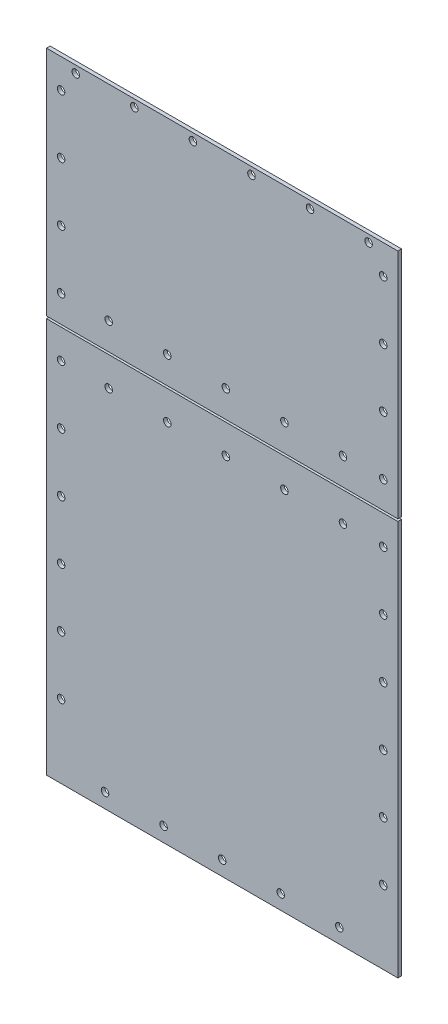
SolidWorks part; units mm, degrees
material "Copper"
ref_plane "Front Plane" through (0, 0, 0) normal (0, 0, 1) x (1, 0, 0)
ref_plane "Top Plane" through (0, 0, 0) normal (0, 1, 0) x (1, 0, 0)
ref_plane "Right Plane" through (0, 0, 0) normal (1, 0, 0) x (0, 0, -1)
sketch "Sketch1" plane through (0, 0, 0) normal (0, 0, 1) x (1, 0, 0)
  line L0 (0, -100.6) -> (152.4, -100.6)
  line L1 (0, 0) -> (152.4, 0)
  line L2 (0, 0) -> (0, -273.05)
  line L3 (0, -273.05) -> (152.4, -273.05)
  line L4 (152.4, 0) -> (152.4, -273.05)
  line L5 (0, -101.6) -> (152.4, -101.6)
  circle A0 centre (6.35, -12.7) radius 1.632
  circle A1 centre (146.05, -12.7) radius 1.632
  circle A2 centre (146.05, -38.1) radius 1.632
  circle A3 centre (146.05, -63.5) radius 1.632
  circle A4 centre (146.05, -88.9) radius 1.632
  circle A5 centre (146.05, -114.3) radius 1.632
  circle A6 centre (146.05, -139.7) radius 1.632
  circle A7 centre (146.05, -165.1) radius 1.632
  circle A8 centre (146.05, -190.5) radius 1.632
  circle A9 centre (146.05, -215.9) radius 1.632
  circle A10 centre (146.05, -241.3) radius 1.632
  circle A11 centre (6.35, -38.1) radius 1.6319
  circle A12 centre (6.35, -63.5) radius 1.6319
  circle A13 centre (6.35, -88.9) radius 1.6319
  circle A14 centre (6.35, -114.3) radius 1.6319
  circle A15 centre (6.35, -139.7) radius 1.6319
  circle A16 centre (6.35, -165.1) radius 1.632
  circle A17 centre (6.35, -190.5) radius 1.632
  circle A18 centre (6.35, -215.9) radius 1.632
  circle A19 centre (6.35, -241.3) radius 1.632
  circle A20 centre (12.7, -3.175) radius 1.632
  circle A21 centre (38.1, -3.175) radius 1.632
  circle A22 centre (63.5, -3.175) radius 1.632
  circle A23 centre (88.9, -3.175) radius 1.632
  circle A24 centre (114.3, -3.175) radius 1.632
  circle A25 centre (139.7, -3.175) radius 1.632
  circle A26 centre (25.4, -266.7) radius 1.632
  circle A27 centre (50.8, -266.7) radius 1.632
  circle A28 centre (76.2, -266.7) radius 1.632
  circle A29 centre (101.6, -266.7) radius 1.632
  circle A30 centre (127, -266.7) radius 1.632
  circle A31 centre (26.99, -88.9) radius 1.6319
  circle A32 centre (26.99, -114.3) radius 1.6319
  circle A33 centre (52.39, -114.3) radius 1.6319
  circle A34 centre (52.39, -88.9) radius 1.6319
  circle A35 centre (77.79, -114.3) radius 1.632
  circle A36 centre (77.79, -88.9) radius 1.632
  circle A37 centre (103.19, -114.3) radius 1.632
  circle A38 centre (103.19, -88.9) radius 1.632
  circle A39 centre (128.59, -114.3) radius 1.632
  circle A40 centre (128.59, -88.9) radius 1.632
  dimension "D3" = 3.2639
  dimension "D1" = 273.05
  dimension "D2" = 152.4
  dimension "D4" = 12.7
  dimension "D5" = 6.35
  dimension "D8" = 6.35
  dimension "D9" = 25.4
  dimension "D10" = 3.175
  dimension "D11" = 12.7
  dimension "D13" = 25.4
  dimension "D14" = 6.35
  dimension "D15" = 25.4
  dimension "D17" = 25.4
  dimension "D18" = 11.7
  dimension "D19" = 1
  dimension "D20" = 26.99
  dimension "D22" = 25.4
  dimension "D6" = 2
  dimension "D7" = 10
  dimension "D12" = 6
  dimension "D16" = 5
  dimension "D21" = 5
extrude "Boss-Extrude1" add sketch "Sketch1" along normal blind 1.5875 contours L4 L1 L2 L0 A25 A24 A23 A22 A21 A20 A13 A12 A11 A4 A3 A2 A1 A0 | L5 L2 L3 L4 A30 A29 A28 A27 A26 A19 A18 A17 A16 A15 A14 A10 A9 A8 A7 A6 A5
equation "\"D18@Sketch1\"=(\"D9@Sketch1\"/2)-1"
